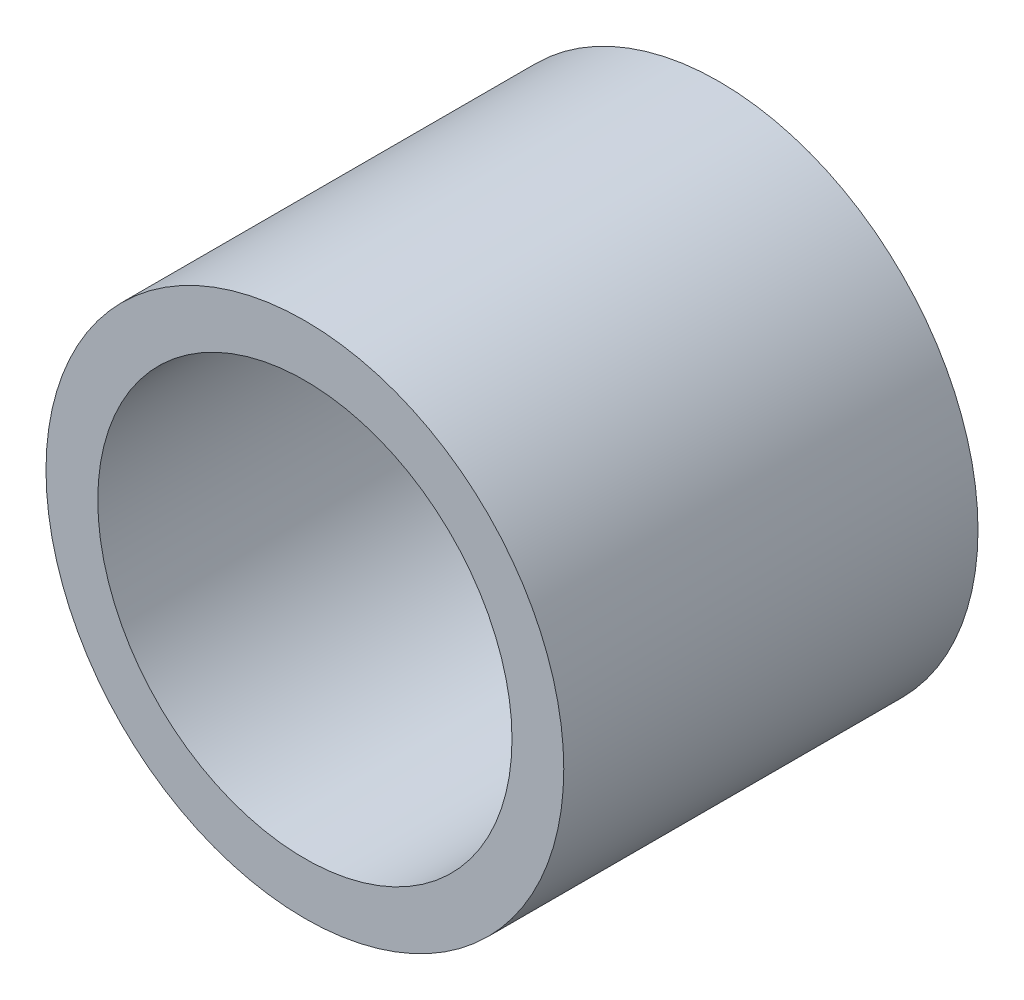
SolidWorks part; units mm, degrees
ref_plane "Front Plane" through (0, 0, 0) normal (0, 0, 1) x (1, 0, 0)
ref_plane "Top Plane" through (0, 0, 0) normal (0, 1, 0) x (1, 0, 0)
ref_plane "Right Plane" through (0, 0, 0) normal (1, 0, 0) x (0, 0, -1)
sketch "Sketch1" plane through (0, 0, 0) normal (0, 0, 1) x (1, 0, 0)
  circle A0 centre (0, 0) radius 1.25
  circle A1 centre (0, 0) radius 1
  dimension "D1" = 2
  dimension "D2" = 2.5
extrude "Boss-Extrude1" add sketch "Sketch1" along normal blind 2
